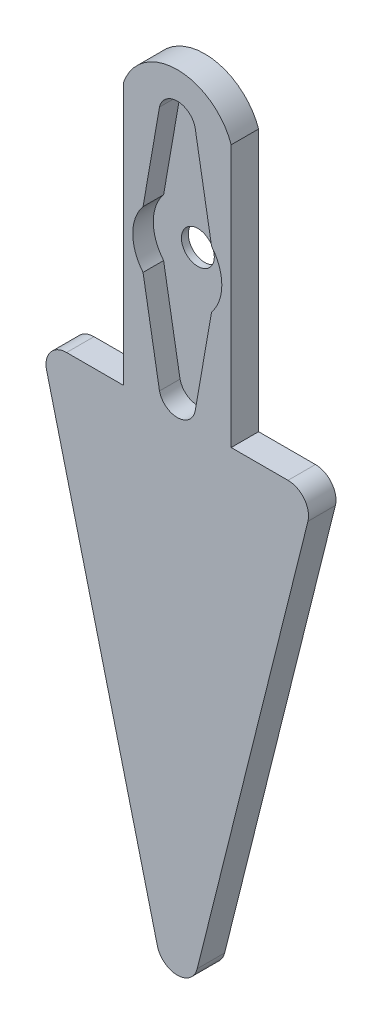
SolidWorks part; units mm, degrees
ref_plane "前基準面" through (0, 0, 0) normal (0, 0, 1) x (1, 0, 0)
ref_plane "上基準面" through (0, 0, 0) normal (0, 1, 0) x (1, 0, 0)
ref_plane "右基準面" through (0, 0, 0) normal (1, 0, 0) x (0, 0, -1)
sketch "草圖1" plane through (0, 0, 0) normal (0, 0, 1) x (1, 0, 0)
  line L1 (0, -55) -> (0, 55) construction
  line L2 (-5, 4.15) -> (-2.6, 17.9428)
  line L3 (2.6, 17.9428) -> (5, 4.15)
  line L4 (2.6, -17.9428) -> (5, -4.15)
  line L5 (-5, -4.15) -> (-2.6, -17.9428)
  line L6 (55, 0) -> (-55, 0) construction
  line L8 (-7.8674, -19.8567) -> (-20, -19.8567)
  line L18 (7.8674, 18.4083) -> (7.8674, -19.8567)
  line L20 (-7.8674, 18.4083) -> (-7.8674, -19.8567)
  line L30 (-20, -19.8567) -> (0, -99.8567)
  line L32 (20, -19.8567) -> (0, -99.8567)
  line L33 (7.8674, -19.8567) -> (20, -19.8567)
  arc A0 (-4.9993, 4.1542) -> (-4.9993, -4.1542) centre (0, 0) ccw
  arc A3 (-2.6, 17.9428) -> (2.6, 17.9428) centre (0, 17.3284) cw
  arc A4 (-2.6, -17.9428) -> (2.6, -17.9428) centre (0, -17.3284) ccw
  arc A5 (4.9993, -4.1542) -> (4.9993, 4.1542) centre (0, 0) ccw
  arc A17 (-7.8674, 18.4083) -> (7.8674, 18.4083) centre (0, 15.6415) cw
  point P10 (0, 20)
  point P27 (0, 0)
  point P28 (0, 0)
  point P29 (0, 0)
  point P30 (0, 0)
  point P31 (-8.1697, -19.8567)
  point P32 (7.8674, 18.4083)
  dimension "D1" = 5
  dimension "D2" = 14
  dimension "D3" = 14
  dimension "D9" = 13
  dimension "D4" = 5
  dimension "D5" = 2.6
  dimension "D6" = 20
  dimension "D7" = 2.6
  dimension "D8" = 20
  dimension "D10" = 38.265
  dimension "D12" = 80
extrude "填料-伸長1" add sketch "草圖1" along normal blind 4
sketch "草圖2" plane through (0, 0, 0) normal (0, 0, 1) x (1, 0, 0)
  line L1 (-3.7023, 20.1723) -> (4.4976, 20.1723)
  line L2 (-6.6467, 17.4711) -> (-6.6467, -20.6283)
  line L3 (-6.6467, -20.6283) -> (7.0328, -20.6283)
  line L4 (7.0328, 17.4076) -> (7.0328, -20.6283)
  circle A0 centre (0, 0) radius 2.4
  arc A1 (-6.6467, 17.4711) -> (-3.7023, 20.1723) centre (-3.3588, 16.8425) cw
  arc A2 (4.4976, 20.1723) -> (7.0328, 17.4076) centre (2.7686, 16.042) cw
extrude "填料-伸長2" add sketch "草圖2" along normal blind 1
fillet "圓角1" radius 3 3 edges at (20, -19.8567, 2) (-20, -19.8567, 2) (0, -99.8567, 2)
